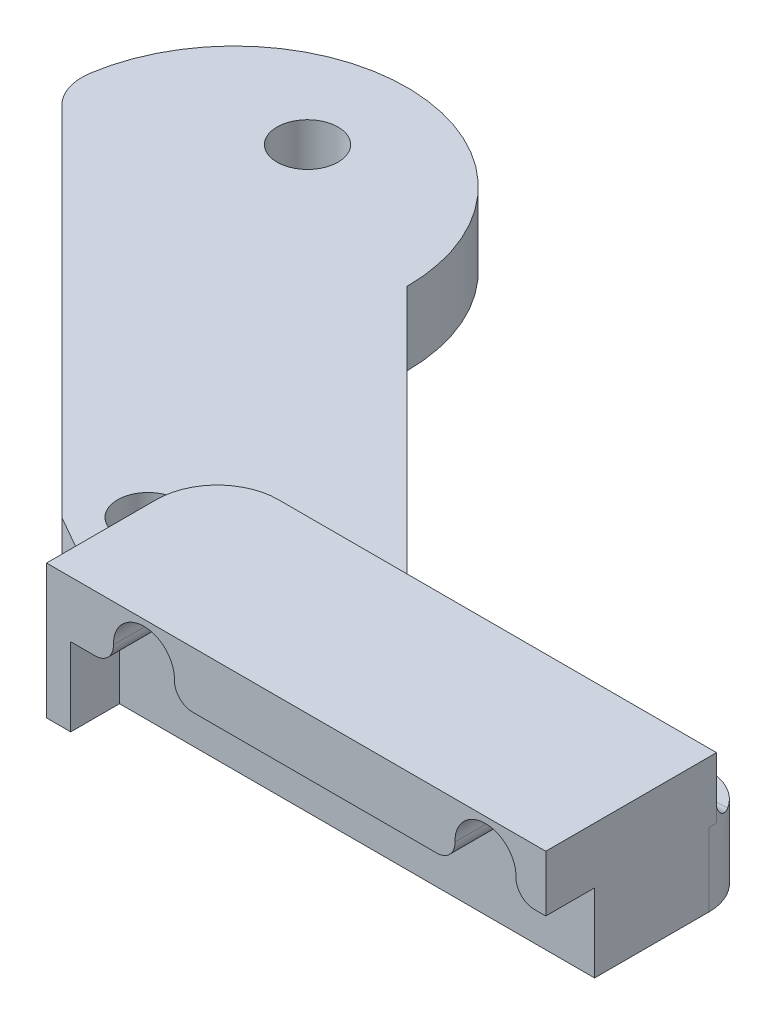
SolidWorks part; units mm, degrees
ref_plane "Front Plane" through (0, 0, 0) normal (0, 0, 1) x (1, 0, 0)
ref_plane "Top Plane" through (0, 0, 0) normal (0, 1, 0) x (1, 0, 0)
ref_plane "Right Plane" through (0, 0, 0) normal (1, 0, 0) x (0, 0, -1)
sketch "Sketch1" plane through (0, 0, 0) normal (0, 1, 0) x (1, 0, 0)
  line L0 (0, 6.35) -> (12.3665, 6.35)
  line L1 (12.3665, 6.35) -> (57.15, 6.35)
  line L2 (6.35, 0) -> (6.35, -10.668)
  line L3 (6.35, -10.668) -> (57.15, -10.668)
  line L4 (57.15, 6.35) -> (57.15, -10.668)
  line L5 (20.5908, 6.35) -> (-7.3492, 34.29)
  line L6 (-4.4901, -4.4901) -> (-43.2703, 34.29)
  line L7 (-4.4901, -4.4901) -> (6.35, -10.668)
  circle A0 centre (0, 0) radius 3.175
  arc A1 (0, 6.35) -> (6.35, 0) centre (0, 0) ccw
  arc A2 (-43.2703, 34.29) -> (-7.3492, 34.29) centre (-25.3097, 34.29) cw
  dimension "D1" = 12.7
  dimension "D2" = 6.35
  dimension "D3" = 6.35
  dimension "D4" = 50.8
  dimension "D5" = 17.018
  dimension "D6" = 45
  dimension "D7" = 25.4
  dimension "D8" = 27.94
extrude "Boss-Extrude1" add sketch "Sketch1" along normal mid plane 7.62 contours A2 L6 A1 L0 L1 L5 | L0 A1 L2 L3 L4 L1 A0 | A1 L7 L2
fillet "Fillet1" radius 5.08 4 edges at (57.15, 0, -6.35) (20.5908, 0, -6.35) (6.35, 0, 10.668) (-43.2703, 0, -34.29)
sketch "Sketch3" plane through (0, 3.81, 0) normal (0, 1, 0) x (1, 0, 0)
  circle A0 centre (-25.3097, 41.91) radius 3.175
  arc A1 (-7.3492, 34.29) -> (-43.0622, 37.016) centre (-25.3097, 34.29) ccw construction
  arc A2 (-7.3492, 34.29) -> (-43.0622, 37.016) centre (-25.3097, 34.29) ccw
  dimension "D2" = 6.35
  dimension "D1" = 7.62
extrude "Cut-Extrude2" cut sketch "Sketch3" against normal through all contours A0
sketch "Sketch4" plane through (0, 3.81, 0) normal (0, 1, 0) x (1, 0, 0)
  line L1 (57.15, -10.668) -> (7.6959, -10.668)
  line L2 (57.15, -10.668) -> (57.15, 2.032)
  line L3 (57.15, 2.032) -> (11.5306, 2.032)
  line L4 (5.1806, -10.0016) -> (5.1806, -4.318)
  arc A0 (5.1806, -10.0016) -> (7.6959, -10.668) centre (7.6959, -5.588) ccw construction
  arc A1 (5.1806, -10.0016) -> (7.6959, -10.668) centre (7.6959, -5.588) ccw
  arc A2 (11.5306, 2.032) -> (5.1806, -4.318) centre (11.5306, -4.318) ccw
  dimension "D2" = 6.35
  dimension "D1" = 12.7
extrude "Boss-Extrude2" add sketch "Sketch4" along normal blind 6.35
sketch "Sketch6" plane through (0, 0, 10.668) normal (0, 0, 1) x (1, 0, 0)
  line L0 (7.6959, 10.16) -> (7.6959, -3.81) construction
  line L1 (7.6959, 10.16) -> (57.15, 10.16) construction
  circle A0 centre (15.3159, 6.35) radius 2.286
  circle A1 centre (50.8759, 6.35) radius 2.286
  dimension "D1" = 4.572
  dimension "D2" = 4.572
  dimension "D3" = 35.56
  dimension "D4" = 7.62
  dimension "D5" = 3.81
extrude "Cut-Extrude3" cut sketch "Sketch6" against normal blind 6.35
sketch "Sketch7" plane through (0, 0, 10.668) normal (0, 0, 1) x (1, 0, 0)
  line L0 (57.15, 10.16) -> (57.15, -3.81) construction
  line L1 (7.6959, 10.16) -> (57.15, 10.16)
  line L2 (7.6959, 10.16) -> (7.6959, 4.318)
  line L3 (7.6959, 4.318) -> (57.15, 4.318)
  line L4 (57.15, 10.16) -> (57.15, 4.318)
  circle A4 centre (15.3159, 6.35) radius 3.175
  circle A5 centre (50.8759, 6.35) radius 3.175
  circle M3 centre (15.3159, 6.35) radius 2.286
  circle M4 centre (50.8759, 6.35) radius 2.286
  line M5 (57.15, -3.81) -> (57.15, 10.16)
  line M6 (57.15, 10.16) -> (7.6959, 10.16)
  line M7 (7.6959, 10.16) -> (7.6959, -3.81)
  dimension "D2" = 6.35
  dimension "D3" = 6.35
  dimension "D1" = 5.842
extrude "Boss-Extrude3" add sketch "Sketch7" along normal blind 5.08 contours L3 M7 M3 M4 M5 M6
fillet "Fillet2" radius 1.905 4 edges at (53.3155, 4.318, 13.208) (48.4364, 4.318, 13.208) (17.7555, 4.318, 13.208) (12.8764, 4.318, 13.208)
fillet "Fillet3" radius 1.905 3 edges at (5.1806, 3.81, 7.1598) (7.0405, 3.81, -0.1721) (34.3116, 3.81, -2.032)
sketch "Sketch8" plane through (0, 3.81, 0) normal (0, 1, 0) x (1, 0, 0)
  line L1 (7.6959, -15.748) -> (5.1806, -15.748)
  line L2 (7.6959, -15.748) -> (7.6959, -10.0016)
  line L3 (7.6959, -10.0016) -> (5.1806, -10.0016)
  line L4 (5.1806, -15.748) -> (5.1806, -10.0016)
  line L5 (7.6959, -10.668) -> (7.6959, -15.748)
  line L6 (7.6959, -15.748) -> (57.15, -15.748)
  line L7 (57.15, -15.748) -> (57.15, 2.032)
  line L8 (57.15, 2.032) -> (11.5306, 2.032)
  line L9 (5.1806, -4.318) -> (5.1806, -10.0016)
  line L10 (7.6959, -10.668) -> (7.6959, -15.748)
  line L11 (7.6959, -15.748) -> (57.15, -15.748)
  line L12 (57.15, -15.748) -> (57.15, 2.032)
  line L13 (57.15, 2.032) -> (11.5306, 2.032)
  line L14 (5.1806, -4.318) -> (5.1806, -10.0016)
  arc A2 (5.1806, -10.0016) -> (7.6959, -10.668) centre (7.6959, -5.588) ccw
  arc A3 (11.5306, 2.032) -> (5.1806, -4.318) centre (11.5306, -4.318) ccw
  arc A4 (5.1806, -10.0016) -> (7.6959, -10.668) centre (7.6959, -5.588) ccw
  arc A5 (11.5306, 2.032) -> (5.1806, -4.318) centre (11.5306, -4.318) ccw
  dimension "D1" = 0
extrude "Boss-Extrude4" add sketch "Sketch8" along normal up to surface and the other way up to surface contours A4 L4 L1 L2 up to face at (21.4607, 10.16, 7.324) other way up to face at (-25.3097, -3.81, -38.735)
